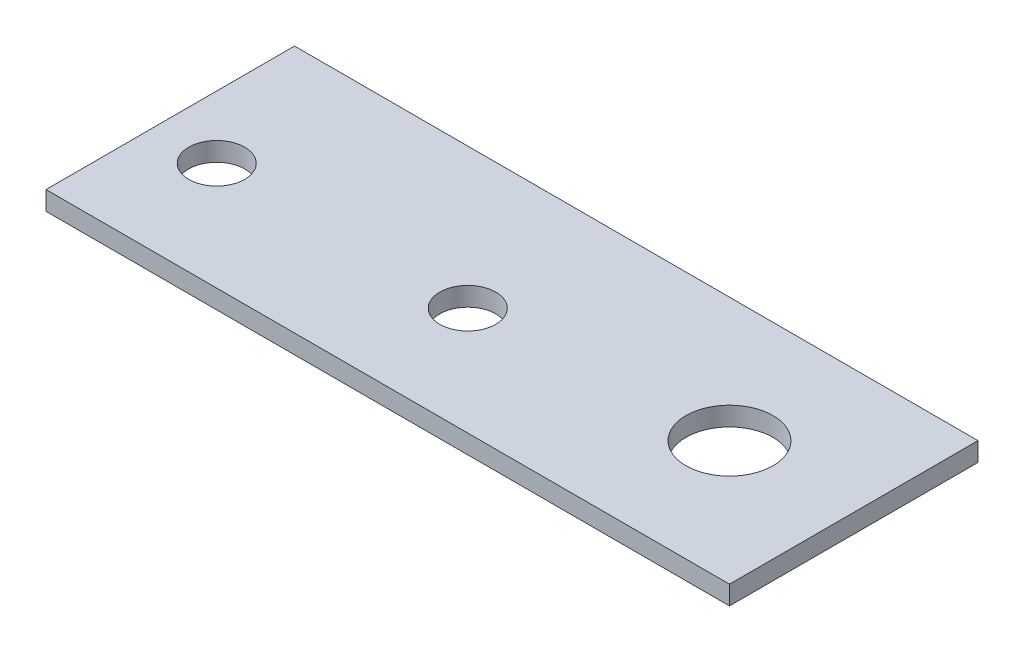
SolidWorks part; units mm, degrees
ref_plane "Front Plane" through (0, 0, 0) normal (0, 0, 1) x (1, 0, 0)
ref_plane "Top Plane" through (0, 0, 0) normal (0, 1, 0) x (1, 0, 0)
ref_plane "Right Plane" through (0, 0, 0) normal (1, 0, 0) x (0, 0, -1)
sketch "Sketch1" plane through (0, 0, 0) normal (0, 1, 0) x (1, 0, 0)
  line L1 (-13.75, 5) -> (13.75, 5)
  line L2 (-13.75, 5) -> (-13.75, -5)
  line L3 (-13.75, -5) -> (13.75, -5)
  line L4 (13.75, 5) -> (13.75, -5)
  line L5 (-13.75, 5) -> (13.75, -5) construction
  line L6 (-13.75, -5) -> (13.75, 5) construction
  circle A0 centre (8.75, 0) radius 1.75
  circle A1 centre (-1.13, -0.65) radius 1.125
  circle A2 centre (-11.23, -0.65) radius 1.125
  point P0 (0, 0)
  dimension "D5" = 3.5
  dimension "D6" = 2.25
  dimension "D7" = 2.25
  dimension "D1" = 10
  dimension "D2" = 27.5
  dimension "D3" = 10.1
  dimension "D4" = 5
  dimension "D8" = 14.88
  dimension "D9" = 0.65
extrude "Boss-Extrude1" add sketch "Sketch1" along normal mid plane 0.76
